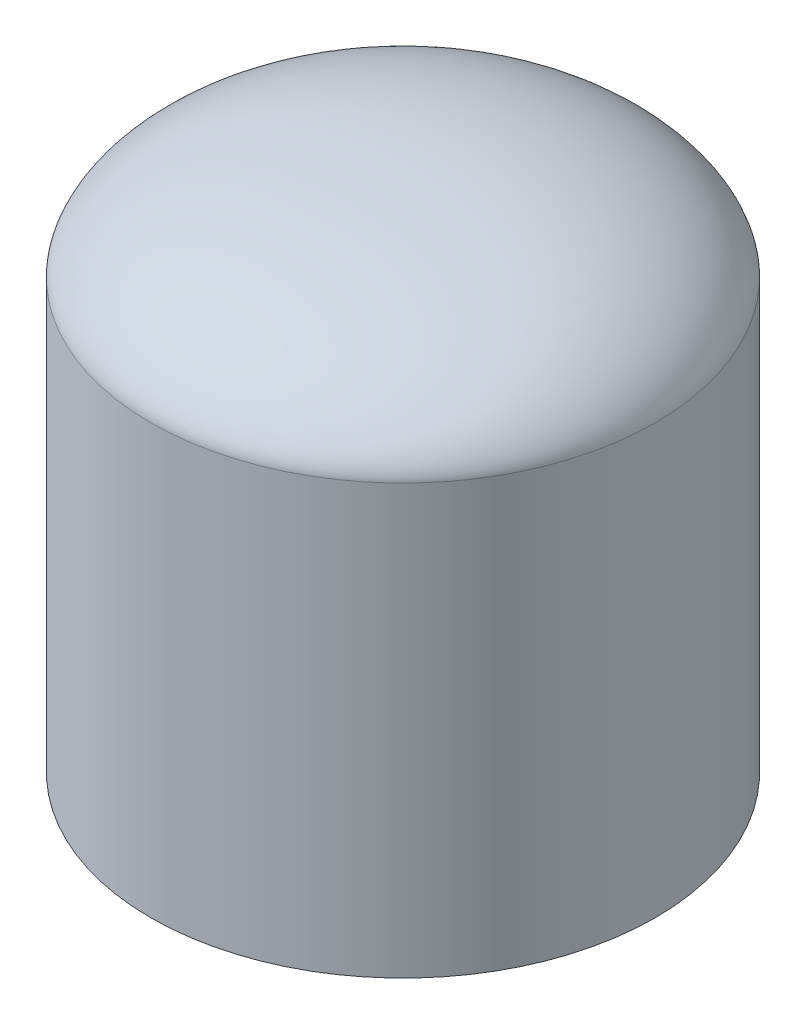
SolidWorks part; units mm, degrees
material "Hêtre"
ref_plane "Plan de face" through (0, 0, 0) normal (0, 0, 1) x (1, 0, 0)
ref_plane "Plan de dessus" through (0, 0, 0) normal (0, 1, 0) x (1, 0, 0)
ref_plane "Plan de droite" through (0, 0, 0) normal (1, 0, 0) x (0, 0, -1)
sketch "Esquisse1" plane through (0, 0, 0) normal (0, 0, 1) x (1, 0, 0)
  line L0 (-5, 0) -> (-5, -8.5)
  line L1 (-5, -8.5) -> (0, -8.5)
  line L3 (-5, 10.7141) -> (-5, 12.2859) construction
  line L4 (-2.6721, 2) -> (2.6721, 2) construction
  line L5 (0, -8.5) -> (0, 2) construction
  line L6 (0, -8.5) -> (0, 2)
  spline S0 degree 3 poles (0, 2) (-3.8147, 2) (-5, 0.454) (-5, 0) knots 0 0 0 0 1 1 1 1
  dimension "D1" = 2
  dimension "D2" = 8.5
  dimension "D3" = 5
  dimension "D4" = 8.5
revolve "Révolution1" add sketch "Esquisse1" angle 360 about L6
